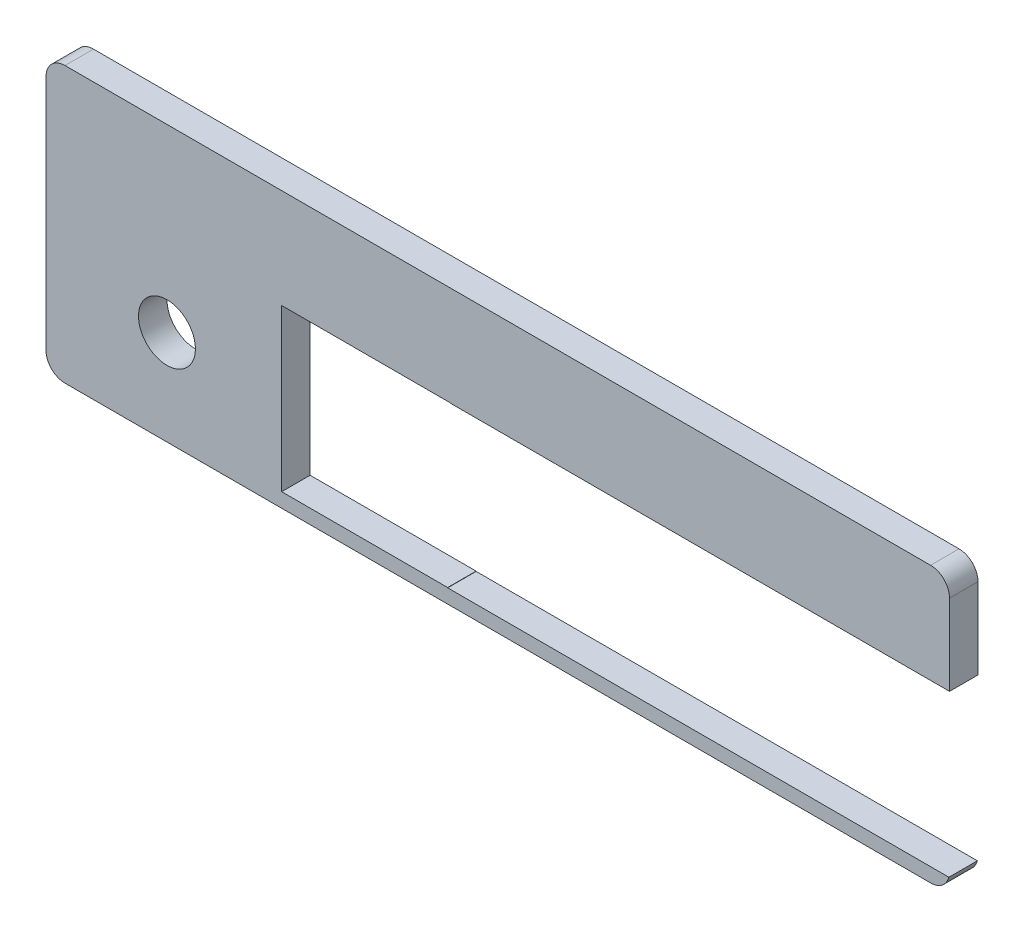
SolidWorks part; units mm, degrees
ref_plane "Front Plane" through (0, 0, 0) normal (0, 0, 1) x (1, 0, 0)
ref_plane "Top Plane" through (0, 0, 0) normal (0, 1, 0) x (1, 0, 0)
ref_plane "Right Plane" through (0, 0, 0) normal (1, 0, 0) x (0, 0, -1)
sketch "Sketch1" plane through (0, 0, 0) normal (0, 0, 1) x (1, 0, 0)
  line L13 (44, 19.75) -> (-47.25, 19.75)
  line L14 (-49.25, 17.75) -> (-49.25, -7.25)
  line L15 (-47.25, -9.25) -> (44, -9.25)
  line L16 (46, 9.2363) -> (46, 17.75)
  line L20 (-6.5925, 9.2363) -> (-6.5925, 9.2637)
  line L21 (-6.5925, 9.2637) -> (-24.4064, 9.2637)
  line L22 (-24.4064, 9.2637) -> (-24.4064, -7.7363)
  line L23 (-24.4064, -7.7363) -> (-6.5925, -7.7363)
  line L32 (-6.9075, -7.7363) -> (-6.9075, -7.7637)
  line L33 (-6.9075, -7.7637) -> (10.9064, -7.7637)
  line L34 (45.9064, 9.2363) -> (46, 9.2363)
  line L35 (10.9064, 9.2363) -> (-6.9075, 9.2363)
  line L44 (45.9064, -7.7637) -> (45.9329, -7.7637)
  line L45 (10.5925, -7.7637) -> (28.4064, -7.7637)
  line L47 (28.4064, 9.2363) -> (10.5925, 9.2363)
  line L57 (28.0925, -7.7637) -> (45.9064, -7.7637)
  line L59 (45.9064, 9.2363) -> (28.0925, 9.2363)
  circle A0 centre (-36.5, 0.75) radius 3
  arc A12 (-47.25, 19.75) -> (-49.25, 17.75) centre (-47.25, 17.75) ccw
  arc A13 (-49.25, -7.25) -> (-47.25, -9.25) centre (-47.25, -7.25) ccw
  arc A14 (44, -9.25) -> (45.9329, -7.7637) centre (44, -7.25) ccw
  arc A15 (46, 17.75) -> (44, 19.75) centre (44, 17.75) ccw
  dimension "D1" = 6
  dimension "D2" = 91.25
  dimension "D3" = 25
extrude "Boss-Extrude1" add sketch "Sketch1" along normal blind 3 contours L16 A15 L13 A12 L14 A13 L15 A14 L44 L57 L45 L33 L32 L23 L22 L21 L20 L35 L47 L59 L34 A0
